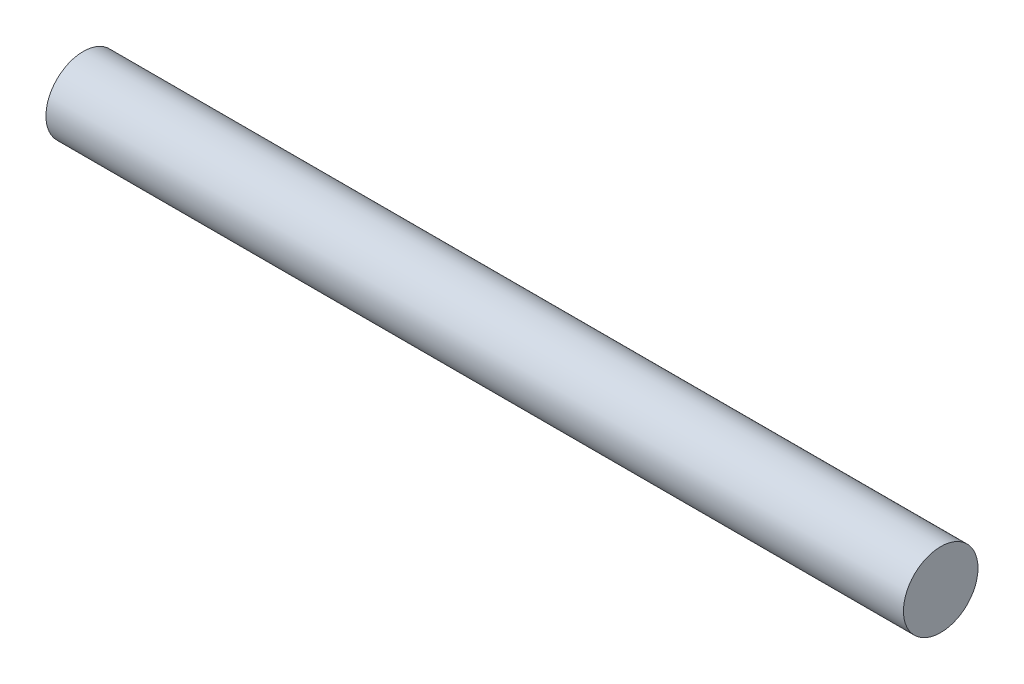
SolidWorks part; units mm, degrees
ref_plane "Front Plane" through (0, 0, 0) normal (0, 0, 1) x (1, 0, 0)
ref_plane "Top Plane" through (0, 0, 0) normal (0, 1, 0) x (1, 0, 0)
ref_plane "Right Plane" through (0, 0, 0) normal (1, 0, 0) x (0, 0, -1)
sketch "Sketch1" plane through (0, 0, 0) normal (1, 0, 0) x (0, 0, -1)
  circle A0 centre (0, 0) radius 1
  dimension "D1" = 2
extrude "Boss-Extrude1" add sketch "Sketch1" along normal mid plane 23
